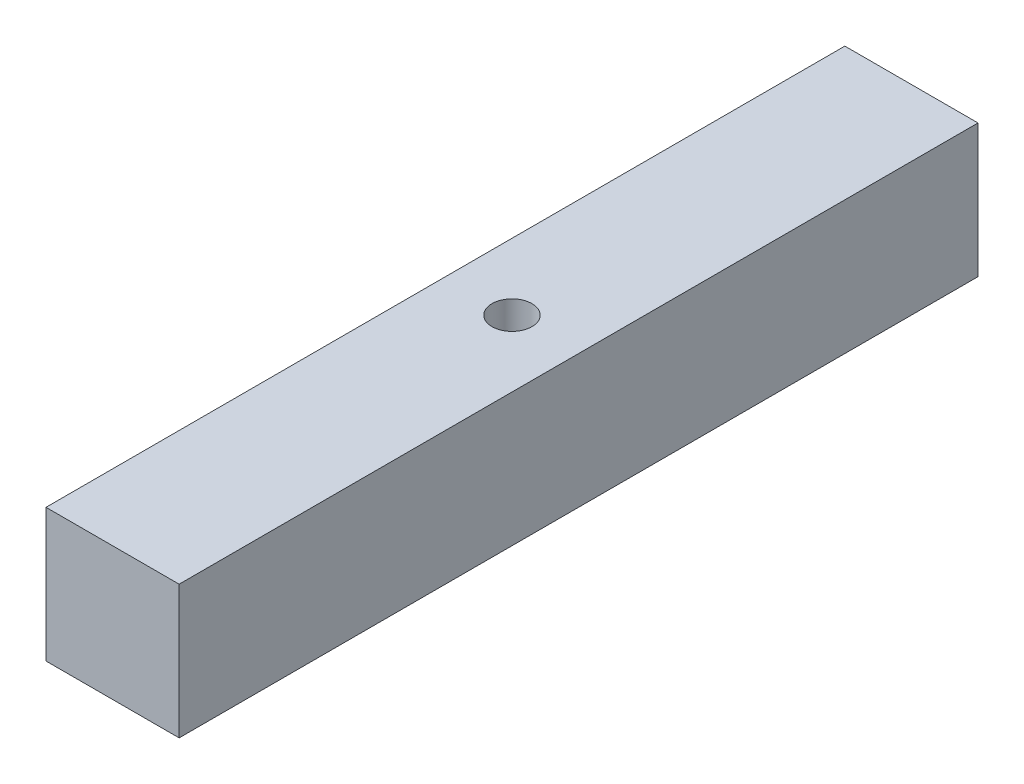
SolidWorks part; units mm, degrees
material "Ceramic Porcelain"
ref_plane "Front Plane" through (0, 0, 0) normal (0, 0, 1) x (1, 0, 0)
ref_plane "Top Plane" through (0, 0, 0) normal (0, 1, 0) x (1, 0, 0)
ref_plane "Right Plane" through (0, 0, 0) normal (1, 0, 0) x (0, 0, -1)
sketch "Sketch1" plane through (0, 0, 0) normal (0, 0, 1) x (1, 0, 0)
  line L1 (500, -300) -> (450, -300)
  line L2 (500, -300) -> (500, -250)
  line L3 (500, -250) -> (450, -250)
  line L4 (450, -300) -> (450, -250)
  dimension "D1" = 50
extrude "Boss-Extrude1" add sketch "Sketch1" along normal blind 300
sketch "Sketch2" plane through (0, -250, 0) normal (0, 1, 0) x (1, 0, 0)
  line L0 (475, 0) -> (475, -300) construction
  line L1 (500, 0) -> (450, 0) construction
  line L2 (500, -300) -> (450, -300) construction
  circle A0 centre (475, -150) radius 7.5
  dimension "D1" = 15
extrude "Cut-Extrude1" cut sketch "Sketch2" against normal blind 15
